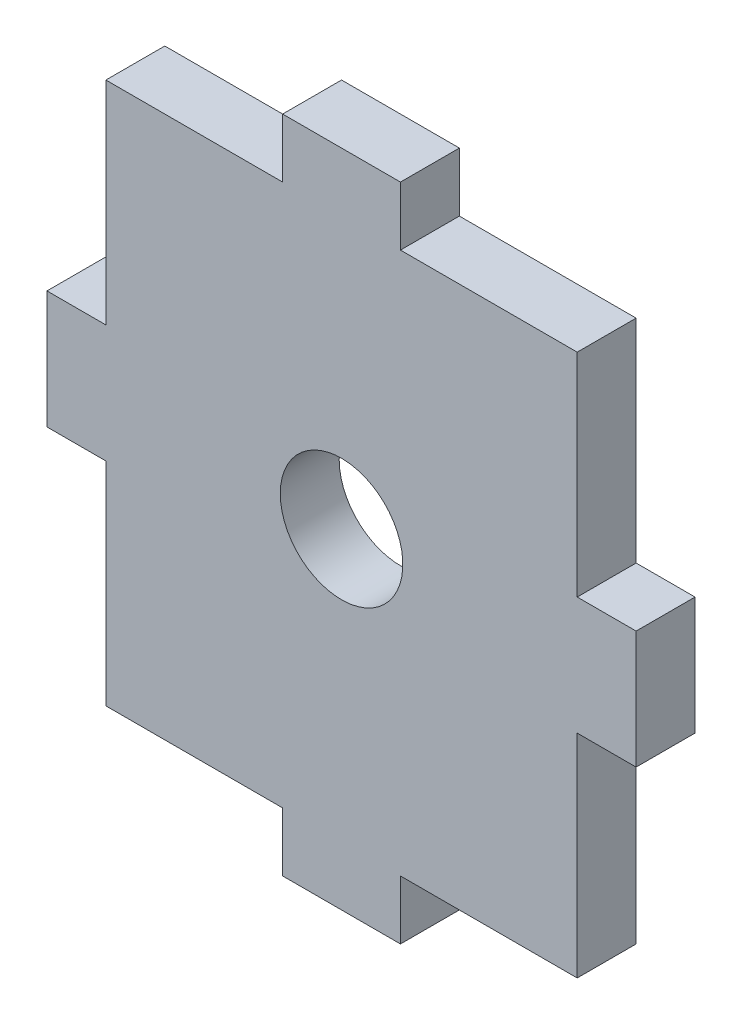
SolidWorks part; units mm, degrees
ref_plane "Front Plane" through (0, 0, 0) normal (0, 0, 1) x (1, 0, 0)
ref_plane "Top Plane" through (0, 0, 0) normal (0, 1, 0) x (1, 0, 0)
ref_plane "Right Plane" through (0, 0, 0) normal (1, 0, 0) x (0, 0, -1)
sketch "Sketch1" plane through (0, 0, 0) normal (0, 0, 1) x (1, 0, 0)
  line L0 (0, -17.78) -> (0, 17.78) construction
  line L1 (-12.7, 14.605) -> (-3.175, 14.605)
  line L2 (-12.7, 14.605) -> (-12.7, 3.175)
  line L3 (0, 0) -> (35.3222, 0) construction
  line L4 (15.875, 3.175) -> (15.875, -3.175)
  line L5 (12.7, 3.175) -> (15.875, 3.175)
  line L6 (3.175, 17.78) -> (3.175, 14.605)
  line L7 (-3.175, 17.78) -> (3.175, 17.78)
  line L8 (-3.175, 17.78) -> (-3.175, 14.605)
  line L9 (12.7, 14.605) -> (12.7, 3.175)
  line L10 (12.7, 14.605) -> (3.175, 14.605)
  line L11 (-12.7, 3.175) -> (-15.875, 3.175)
  line L12 (-12.7, -3.175) -> (-15.875, -3.175)
  line L13 (12.7, -14.605) -> (3.175, -14.605)
  line L14 (-15.875, 3.175) -> (-15.875, -3.175)
  line L15 (12.7, -14.605) -> (12.7, -3.175)
  line L16 (-3.175, -17.78) -> (-3.175, -14.605)
  line L17 (-3.175, -17.78) -> (3.175, -17.78)
  line L18 (3.175, -17.78) -> (3.175, -14.605)
  line L19 (12.7, -3.175) -> (15.875, -3.175)
  line L20 (-12.7, -14.605) -> (-12.7, -3.175)
  line L21 (-12.7, -14.605) -> (-3.175, -14.605)
  point P18 (-15.875, 0)
  point P26 (15.875, 0)
  dimension "D1" = 31.75
  dimension "D2" = 3.175
  dimension "D3" = 3.175
  dimension "D4" = 35.56
  dimension "D5" = 3.175
  dimension "D6" = 3.175
extrude "Extrude1" add sketch "Sketch1" along normal blind 3.175
sketch "Sketch2" plane through (0, 0, 0) normal (0, 0, -1) x (-1, 0, 0)
  circle A0 centre (0, 0) radius 3.302
  dimension "D1" = 6.604
extrude "Cut-Extrude1" cut sketch "Sketch2" against normal blind 3.175
